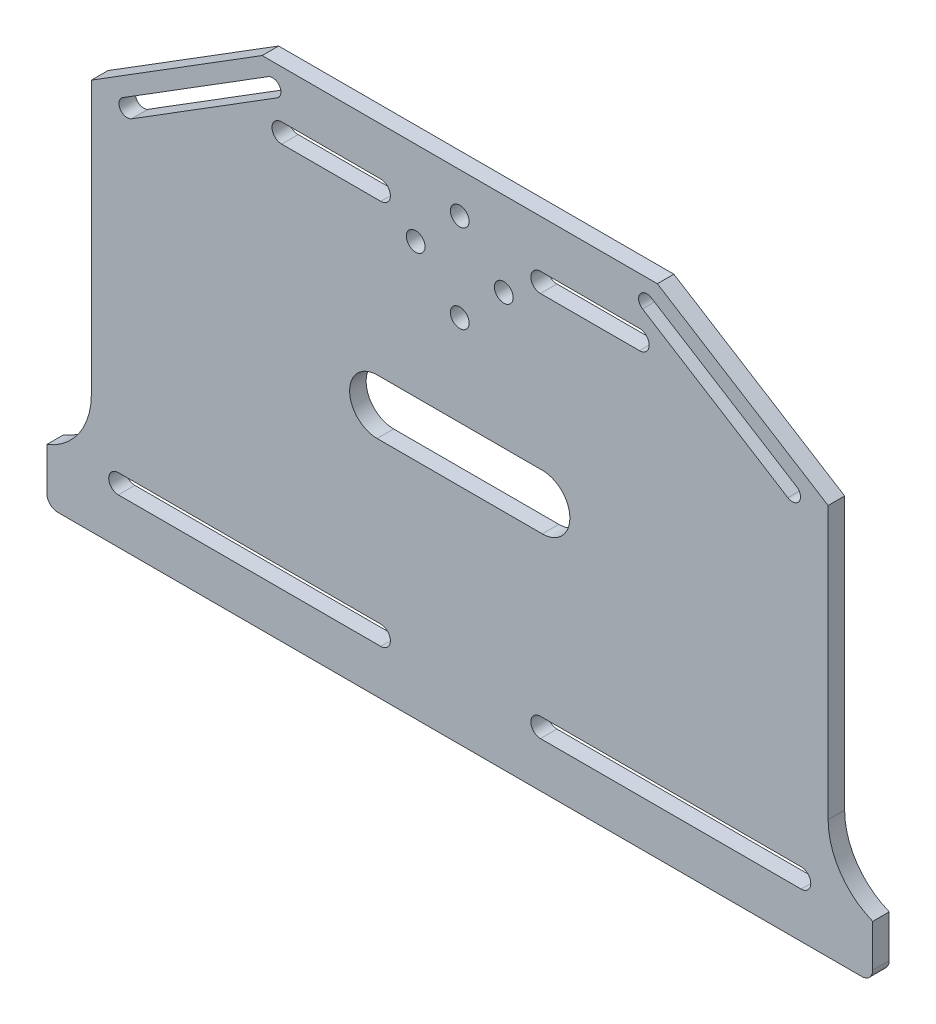
SolidWorks part; units mm, degrees
ref_plane "前视基准面" through (0, 0, 0) normal (0, 0, 1) x (1, 0, 0)
ref_plane "上视基准面" through (0, 0, 0) normal (0, 1, 0) x (1, 0, 0)
ref_plane "右视基准面" through (0, 0, 0) normal (1, 0, 0) x (0, 0, -1)
sketch "草图1" plane through (0, 0, 0) normal (0, 0, 1) x (1, 0, 0)
  line L0 (0, 148.5) -> (0, -94.9538) construction
  line L1 (105, -148.5) -> (-105, -148.5) construction
  line L2 (105, -148.5) -> (105, 148.5) construction
  line L3 (105, 148.5) -> (-105, 148.5) construction
  line L4 (-105, -148.5) -> (-105, 148.5) construction
  line L5 (105, -148.5) -> (-105, 148.5) construction
  line L6 (105, 148.5) -> (-105, -148.5) construction
  line L7 (35.8892, 121.6645) -> (-35.8892, 121.6645)
  line L8 (-35.8892, 121.6645) -> (-66.9017, 102.292)
  line L9 (-75, 40.9339) -> (-75, 31.2613)
  line L10 (-66.9017, 102.292) -> (-66.9017, 52.8701)
  line L11 (75, 40.9339) -> (75, 31.2613)
  line L12 (66.9017, 102.292) -> (66.9017, 52.8701)
  line L13 (35.8892, 121.6645) -> (66.9017, 102.292)
  line L14 (-75, 31.2613) -> (75, 31.2613)
  line L15 (-60, -148.5) -> (-60, -91.8129)
  line L16 (-75, 23.94) -> (75, 23.94)
  line L17 (-75, 23.94) -> (-75, 10.5626)
  line L18 (-38.8455, -105.5906) -> (-66.4608, -113.7617)
  line L19 (-66.4608, -113.7617) -> (-70.1743, -102.7328)
  line L20 (75, 23.94) -> (75, 10.5626)
  line L21 (66.4608, -113.7617) -> (70.1743, -102.7328)
  line L22 (38.8455, -105.5906) -> (66.4608, -113.7617)
  line L23 (-105, 93.0519) -> (105, 93.0519)
  line L24 (-105, 63.0519) -> (105, 63.0519)
  line L25 (-105, -90.0629) -> (-70.5337, -90.0629)
  line L26 (-105, -60.0629) -> (-67.4027, -60.0629)
  line L27 (60, -148.5) -> (60, 148.5)
  line L28 (-60, -58.3129) -> (-45, -58.3129)
  line L29 (-60, -61.8129) -> (-45, -61.8129)
  line L30 (-36, -58.3129) -> (-21, -58.3129)
  line L31 (-36, -61.8129) -> (-21, -61.8129)
  line L32 (-60, -88.3129) -> (-45, -88.3129)
  line L33 (-60, -91.8129) -> (-45, -91.8129)
  line L34 (-36, -88.3129) -> (-21, -88.3129)
  line L35 (-36, -91.8129) -> (-21, -91.8129)
  line L36 (-60, -58.3129) -> (-60, 148.5)
  line L37 (-19.25, -90.0629) -> (105, -90.0629)
  line L38 (-19.25, -60.0629) -> (19.25, -60.0629)
  line L39 (-60, -88.3129) -> (-60, -61.8129)
  line L40 (21, -58.3129) -> (36, -58.3129)
  line L41 (45, -58.3129) -> (60, -58.3129)
  line L42 (60, -61.8129) -> (45, -61.8129)
  line L43 (36, -61.8129) -> (21, -61.8129)
  line L44 (21, -88.3129) -> (36, -88.3129)
  line L45 (21, -91.8129) -> (36, -91.8129)
  line L46 (45, -88.3129) -> (60, -88.3129)
  line L47 (45, -91.8129) -> (60, -91.8129)
  line L48 (37.75, -60.0629) -> (43.25, -60.0629)
  line L49 (58.25, -60.0629) -> (105, -60.0629)
  line L50 (-60, 94.8019) -> (-45, 94.8019)
  line L51 (-36, 94.8019) -> (-21, 94.8019)
  line L52 (-60, 91.3019) -> (-45, 91.3019)
  line L53 (-36, 91.3019) -> (-21, 91.3019)
  line L54 (-60, 64.8019) -> (-45, 64.8019)
  line L55 (-60, 61.3019) -> (-45, 61.3019)
  line L56 (-36, 64.8019) -> (-21, 64.8019)
  line L57 (-36, 61.3019) -> (-21, 61.3019)
  line L58 (21, 94.8019) -> (36, 94.8019)
  line L59 (21, 91.3019) -> (36, 91.3019)
  line L60 (45, 94.8019) -> (60, 94.8019)
  line L61 (45, 91.3019) -> (60, 91.3019)
  line L62 (21, 61.3019) -> (36, 61.3019)
  line L63 (21, 64.8019) -> (36, 64.8019)
  line L64 (45, 61.3019) -> (60, 61.3019)
  line L65 (45, 64.8019) -> (60, 64.8019)
  line L66 (-33.1709, -104.7687) -> (33.1709, -104.7687)
  line L67 (0, -104.7687) -> (0, -148.5) construction
  arc A0 (-75, 40.9339) -> (-66.9017, 52.8701) centre (-79.7474, 52.8701) ccw
  arc A1 (75, 40.9339) -> (66.9017, 52.8701) centre (79.7474, 52.8701) cw
  arc A3 (-60, -88.3129) -> (-60, -91.8129) centre (-60, -90.0629) ccw
  arc A4 (-60, -58.3129) -> (-60, -61.8129) centre (-60, -60.0629) ccw
  circle A5 centre (-60, 63.0519) radius 1.75
  circle A6 centre (-60, 93.0519) radius 1.75
  circle A7 centre (60, 93.0519) radius 1.75
  circle A8 centre (60, 63.0519) radius 1.75
  arc A9 (60, -91.8129) -> (60, -88.3129) centre (60, -90.0629) ccw
  arc A10 (60, -61.8129) -> (60, -58.3129) centre (60, -60.0629) ccw
  arc A11 (-36, -58.3129) -> (-36, -61.8129) centre (-36, -60.0629) ccw
  arc A12 (-36, -88.3129) -> (-36, -91.8129) centre (-36, -90.0629) ccw
  arc A13 (36, -61.8129) -> (36, -58.3129) centre (36, -60.0629) ccw
  arc A14 (36, -91.8129) -> (36, -88.3129) centre (36, -90.0629) ccw
  arc A15 (-45, -61.8129) -> (-45, -58.3129) centre (-45, -60.0629) ccw
  arc A16 (-21, -61.8129) -> (-21, -58.3129) centre (-21, -60.0629) ccw
  arc A17 (-45, -91.8129) -> (-45, -88.3129) centre (-45, -90.0629) ccw
  arc A18 (-21, -91.8129) -> (-21, -88.3129) centre (-21, -90.0629) ccw
  arc A19 (45, -58.3129) -> (45, -61.8129) centre (45, -60.0629) ccw
  arc A20 (21, -58.3129) -> (21, -61.8129) centre (21, -60.0629) ccw
  arc A21 (21, -88.3129) -> (21, -91.8129) centre (21, -90.0629) ccw
  arc A22 (45, -88.3129) -> (45, -91.8129) centre (45, -90.0629) ccw
  circle A23 centre (-36, 93.0519) radius 1.75
  circle A24 centre (-36, 63.0519) radius 1.75
  circle A25 centre (36, 93.0519) radius 1.75
  circle A26 centre (36, 63.0519) radius 1.75
  circle A27 centre (-45, 93.0519) radius 1.75
  circle A28 centre (-21, 93.0519) radius 1.75
  circle A29 centre (-45, 63.0519) radius 1.75
  circle A30 centre (-21, 63.0519) radius 1.75
  circle A31 centre (21, 93.0519) radius 1.75
  circle A32 centre (21, 63.0519) radius 1.75
  circle A33 centre (45, 93.0519) radius 1.75
  circle A34 centre (45, 63.0519) radius 1.75
  arc A35 (33.1709, -104.7687) -> (38.8455, -105.5906) centre (33.1709, -124.7687) cw
  arc A36 (-33.1709, -104.7687) -> (-38.8455, -105.5906) centre (-33.1709, -124.7687) ccw
  spline S0 degree 3 poles (-75, 10.5626) (-72.6959, 1.9073) (-70.3396, -13.3728) (-67.1028, -43.6255) (-66.7657, -72.9327) (-71.8903, -95.1489) (-70.1743, -102.7328) knots 0 0 0 0 0.235247 0.406294 0.801186 1 1 1 1
  spline S1 degree 3 poles (75, 10.5626) (72.6959, 1.9073) (70.3396, -13.3728) (67.1028, -43.6255) (66.7657, -72.9327) (71.8903, -95.1489) (70.1743, -102.7328) knots 0 0 0 0 0.235247 0.406294 0.801186 1 1 1 1
  point P0 (0, 0)
  point P27 (0, 121.6645)
  point P42 (0, -94.0966)
  dimension "D1" = 60
  dimension "D4" = 20
  dimension "D5" = 24
  dimension "D7" = 24
  dimension "D9" = 15
  dimension "D10" = 15
  dimension "D13" = 24
  dimension "D17" = 15
  dimension "D2" = 30
  dimension "D3" = 30
  dimension "D6" = 24
  dimension "D8" = 24
  dimension "D11" = 15
  dimension "D12" = 15
  dimension "D14" = 24
  dimension "D15" = 24
  dimension "D16" = 24
  dimension "D18" = 15
  dimension "D19" = 15
  dimension "D20" = 15
  dimension "D21" = 15
  dimension "D22" = 15
  dimension "D23" = 15
  dimension "D24" = 15
  dimension "D25" = 15
  dimension "D26" = 15
  dimension "D27" = 15
  dimension "D28" = 15
  dimension "D29" = 3.5
  dimension "D30" = 3.5
  dimension "D31" = 3.5
extrude "凸台-拉伸1" add sketch "草图1" along normal blind 3
sketch "草图7" plane through (0, 0, 0) normal (0, 0, -1) x (-1, 0, 0)
  line L0 (0, 121.6645) -> (0, -104.7687) construction
  line L1 (-35.8892, 121.6645) -> (35.8892, 121.6645) construction
  line L2 (33.1709, -104.7687) -> (-33.1709, -104.7687) construction
  line L3 (0, 41.2613) -> (-21, 41.2613) construction
  line L4 (0, 41.2613) -> (21, 41.2613) construction
  line L5 (0, 13.94) -> (-21, 13.94) construction
  line L6 (0, 13.94) -> (21, 13.94) construction
  line L7 (75, 23.94) -> (-75, 23.94) construction
  line L8 (75, 31.2613) -> (-75, 31.2613) construction
  circle A0 centre (-21, 41.2613) radius 1.75
  circle A1 centre (21, 41.2613) radius 1.75
  circle A2 centre (-21, 13.94) radius 2.25
  circle A3 centre (21, 13.94) radius 2.25
  dimension "D1" = 10
  dimension "D2" = 10
extrude "切除-拉伸2" cut sketch "草图7" against normal through all
sketch "草图9" plane through (0, 0, 3) normal (0, 0, 1) x (1, 0, 0)
  line L0 (-70.7828, -98.747) -> (70.7828, -98.747) construction
  line L1 (0, -98.747) -> (0, -104.7687) construction
  line L2 (55, -100.497) -> (20, -100.497)
  line L3 (-55, -96.997) -> (-20, -96.997)
  line L4 (-55, -100.497) -> (-20, -100.497)
  line L5 (-33.1709, -104.7687) -> (33.1709, -104.7687) construction
  line L6 (55, -96.997) -> (20, -96.997)
  arc A0 (-55, -96.997) -> (-55, -100.497) centre (-55, -98.747) ccw
  arc A1 (-20, -100.497) -> (-20, -96.997) centre (-20, -98.747) ccw
  arc A2 (20, -100.497) -> (20, -96.997) centre (20, -98.747) cw
  arc A3 (55, -96.997) -> (55, -100.497) centre (55, -98.747) cw
  spline S0 degree 3 poles (-75, 10.5626) (-72.6959, 1.9073) (-70.3396, -13.3728) (-67.1028, -43.6255) (-66.7657, -72.9327) (-71.8903, -95.1489) (-70.1743, -102.7328) knots 0 0 0 0 0.235247 0.406294 0.801186 1 1 1 1 construction
  spline S1 degree 3 poles (75, 10.5626) (72.6959, 1.9073) (70.3396, -13.3728) (67.1028, -43.6255) (66.7657, -72.9327) (71.8903, -95.1489) (70.1743, -102.7328) knots 0 0 0 0 0.235247 0.406294 0.801186 1 1 1 1 construction
  dimension "D1" = 35
  dimension "D2" = 20
extrude "切除-拉伸4" cut sketch "草图9" against normal blind 3
sketch "草图10" plane through (0, 0, 3) normal (0, 0, 1) x (1, 0, 0)
  line L0 (-21, -60.0629) -> (-21, -90.0629) construction
  line L1 (21, -60.0629) -> (21, -90.0629) construction
  line L2 (-21, -75.0629) -> (-17.5, -75.0629) construction
  line L4 (12.5, -80.0629) -> (-12.5, -80.0629)
  line L6 (12.5, -70.0629) -> (-12.5, -70.0629)
  line L11 (17.5, -75.0629) -> (21, -75.0629) construction
  arc A0 (-12.5, -70.0629) -> (-12.5, -80.0629) centre (-12.5, -75.0629) ccw
  arc A1 (12.5, -80.0629) -> (12.5, -70.0629) centre (12.5, -75.0629) ccw
  point P11 (0, -75.0629)
extrude "切除-拉伸5" cut sketch "草图10" against normal blind 3
sketch "草图11" plane through (0, 0, 3) normal (0, 0, 1) x (1, 0, 0)
  line L0 (-21, 93.0519) -> (-21, 63.0519) construction
  line L1 (21, 93.0519) -> (21, 63.0519) construction
  line L2 (-21, 78.0519) -> (-20, 78.0519) construction
  line L4 (15, 73.0519) -> (-15, 73.0519)
  line L6 (15, 83.0519) -> (-15, 83.0519)
  line L10 (20, 78.0519) -> (21, 78.0519) construction
  arc A0 (-15, 83.0519) -> (-15, 73.0519) centre (-15, 78.0519) ccw
  arc A1 (15, 73.0519) -> (15, 83.0519) centre (15, 78.0519) ccw
  point P10 (0, 78.0519)
  dimension "D1" = 30
extrude "切除-拉伸8" cut sketch "草图11" against normal blind 3
sketch "草图12" plane through (0, 0, 3) normal (0, 0, 1) x (1, 0, 0)
  line L0 (0, 121.6645) -> (0, 83.0519) construction
  line L1 (35.8892, 121.6645) -> (-35.8892, 121.6645) construction
  line L2 (15, 83.0519) -> (-15, 83.0519) construction
  circle A0 centre (0, 106.3718) radius 11 construction
  circle A1 centre (0, 106.3718) radius 8 construction
  circle A2 centre (0, 114.3718) radius 1.7
  circle A3 centre (0, 98.3718) radius 1.7
  circle A4 centre (8, 106.3718) radius 1.7
  circle A5 centre (-8, 106.3718) radius 1.7
extrude "切除-拉伸9" cut sketch "草图12" against normal blind 3
sketch "草图13" plane through (0, 0, 3) normal (0, 0, 1) x (1, 0, 0)
  line L0 (0, -104.7687) -> (0, -80.0629) construction
  line L1 (-33.1709, -104.7687) -> (33.1709, -104.7687) construction
  line L2 (-12.5, -80.0629) -> (12.5, -80.0629) construction
  circle A0 centre (0, -92.4158) radius 8 construction
  circle A1 centre (0, -84.4158) radius 1.7
  circle A2 centre (8, -92.4158) radius 1.7
  circle A3 centre (0, -100.4158) radius 1.7
  circle A4 centre (-8, -92.4158) radius 1.7
extrude "切除-拉伸11" cut sketch "草图13" against normal blind 3
sketch "草图14" plane through (0, 0, 3) normal (0, 0, 1) x (1, 0, 0)
  line L0 (0, 23.94) -> (0, -104.7687) construction
  line L1 (-55.4755, 8.9197) -> (-55.4755, -46.0803)
  line L2 (-58.9755, 8.9197) -> (-58.9755, -46.0803)
  line L3 (-75, 23.94) -> (75, 23.94) construction
  line L4 (-33.1709, -104.7687) -> (33.1709, -104.7687) construction
  line L5 (58.9755, 8.9197) -> (58.9755, -46.0803)
  line L6 (55.4755, 8.9197) -> (55.4755, -46.0803)
  arc A0 (-55.4755, 8.9197) -> (-58.9755, 8.9197) centre (-57.2255, 8.9197) ccw
  arc A1 (-58.9755, -46.0803) -> (-55.4755, -46.0803) centre (-57.2255, -46.0803) ccw
  arc A2 (58.9755, -46.0803) -> (55.4755, -46.0803) centre (57.2255, -46.0803) cw
  arc A3 (55.4755, 8.9197) -> (58.9755, 8.9197) centre (57.2255, 8.9197) cw
extrude "切除-拉伸12" cut sketch "草图14" against normal through all
fillet "圆角1" radius 2 2 edges at (75, 31.2613, 1.5) (-75, 31.2613, 1.5)
fillet "圆角2" radius 2 2 edges at (-75, 23.94, 1.5) (75, 23.94, 1.5)
sketch "草图15" plane through (0, 0, 0) normal (0, 0, -1) x (-1, 0, 0)
  line L0 (0, 121.6645) -> (0, 31.2613) construction
  line L1 (-35.8892, 121.6645) -> (35.8892, 121.6645) construction
  line L2 (73, 31.2613) -> (-73, 31.2613) construction
  line L3 (-27.5188, 121.6645) -> (-63.6963, 99.0657) construction
  line L4 (-35.8892, 121.6645) -> (-66.9017, 102.292) construction
  line L5 (-61.1842, 102.4035) -> (-34.7748, 118.9006)
  line L6 (-59.5948, 99.8591) -> (-33.1854, 116.3562)
  line L7 (27.5188, 121.6645) -> (63.6963, 99.0657) construction
  line L8 (59.5948, 99.8591) -> (33.1854, 116.3562)
  line L9 (61.1842, 102.4035) -> (34.7748, 118.9006)
  arc A0 (-61.1842, 102.4035) -> (-59.5948, 99.8591) centre (-60.3895, 101.1313) ccw
  arc A1 (-33.1854, 116.3562) -> (-34.7748, 118.9006) centre (-33.9801, 117.6284) ccw
  arc A2 (33.1854, 116.3562) -> (34.7748, 118.9006) centre (33.9801, 117.6284) cw
  arc A3 (61.1842, 102.4035) -> (59.5948, 99.8591) centre (60.3895, 101.1313) cw
extrude "切除-拉伸13" cut sketch "草图15" against normal through all
sketch "草图16" plane through (0, 0, 0) normal (0, 0, -1) x (-1, 0, 0)
  line L0 (0, 121.6645) -> (0, 31.2613) construction
  line L1 (-35.8892, 121.6645) -> (35.8892, 121.6645) construction
  line L2 (73, 31.2613) -> (-73, 31.2613) construction
  line L3 (-21, 41.2613) -> (-66.71, 41.2613) construction
  line L4 (-62, 43.0113) -> (-32, 43.0113)
  line L5 (-62, 39.5113) -> (-32, 39.5113)
  line L6 (21, 41.2613) -> (66.71, 41.2613) construction
  line L7 (62, 39.5113) -> (32, 39.5113)
  line L8 (62, 43.0113) -> (32, 43.0113)
  line L9 (-75, 40.9339) -> (-75, 33.2613) construction
  arc A0 (-62, 43.0113) -> (-62, 39.5113) centre (-62, 41.2613) ccw
  arc A1 (-32, 39.5113) -> (-32, 43.0113) centre (-32, 41.2613) ccw
  arc A2 (32, 39.5113) -> (32, 43.0113) centre (32, 41.2613) cw
  arc A3 (62, 43.0113) -> (62, 39.5113) centre (62, 41.2613) cw
  dimension "D2" = 13
sketch "草图17" plane through (0, 0, 0) normal (0, 0, -1) x (-1, 0, 0)
  text T0 "Y" font "黑体" height in points 72
extrude "切除-拉伸15" cut sketch "草图17" against normal through all
sketch "草图18" plane through (0, 0, 0) normal (0, 0, -1) x (-1, 0, 0)
  text T0 "H" font "黑体" height in points 72
extrude "切除-拉伸16" cut sketch "草图18" against normal through all
sketch "草图20" plane through (0, 0, 0) normal (0, 0, -1) x (-1, 0, 0)
  line L0 (-66.9017, 102.292) -> (-66.9017, 52.8701) construction
  line L1 (-66.9017, 95.8596) -> (66.9017, 95.8596)
  line L2 (-66.9017, 95.8596) -> (-66.9017, 52.8701)
  line L3 (-66.9017, 52.8701) -> (66.9017, 52.8701)
  line L4 (66.9017, 95.8596) -> (66.9017, 52.8701)
extrude "凸台-拉伸2" add sketch "草图20" against normal blind 3
sketch "草图21" plane through (0, 0, 0) normal (0, 0, -1) x (-1, 0, 0)
  line L1 (-64.7663, -56.4228) -> (64.4409, -56.4228)
  line L2 (-64.7663, -56.4228) -> (-64.7663, -95.2117)
  line L3 (-64.7663, -95.2117) -> (64.4409, -95.2117)
  line L4 (64.4409, -56.4228) -> (64.4409, -95.2117)
extrude "凸台-拉伸3" add sketch "草图21" against normal blind 3
sketch "草图22" plane through (0, 0, 0) normal (0, 0, -1) x (-1, 0, 0)
  line L1 (-46.7188, -3.1128) -> (-25.8503, -3.1128)
  line L2 (-46.7188, -3.1128) -> (-46.7188, -34.3233)
  line L3 (-46.7188, -34.3233) -> (-25.8503, -34.3233)
  line L4 (-25.8503, -3.1128) -> (-25.8503, -34.3233)
  line L5 (28.8143, -3.1128) -> (49.8675, -3.1128)
  line L6 (28.8143, -3.1128) -> (28.8143, -33.2152)
  line L7 (28.8143, -33.2152) -> (49.8675, -33.2152)
  line L8 (49.8675, -3.1128) -> (49.8675, -33.2152)
extrude "凸台-拉伸4" add sketch "草图22" against normal blind 3
sketch "草图24" plane through (0, 0, 0) normal (0, 0, -1) x (-1, 0, 0)
  line L1 (-64.9961, 44.3276) -> (-28.6954, 44.3276)
  line L2 (-64.9961, 44.3276) -> (-64.9961, 38.3743)
  line L3 (-64.9961, 38.3743) -> (-28.6954, 38.3743)
  line L4 (-28.6954, 44.3276) -> (-28.6954, 38.3743)
  line L5 (29.2405, 44.3276) -> (65.8315, 44.3276)
  line L6 (29.2405, 44.3276) -> (29.2405, 38.3743)
  line L7 (29.2405, 38.3743) -> (65.8315, 38.3743)
  line L8 (65.8315, 44.3276) -> (65.8315, 38.3743)
extrude "凸台-拉伸5" add sketch "草图24" against normal blind 3
sketch "草图25" plane through (0, 0, 0) normal (0, 0, -1) x (-1, 0, 0)
  line L0 (-32.6582, 113.0113) -> (-14.6582, 113.0113)
  line L1 (-32.6582, 109.5113) -> (-14.6582, 109.5113)
  line L2 (-21, 41.2613) -> (21, 41.2613)
  line L3 (-0.3165, 111.2613) -> (0, 41.2613) construction
  line L4 (14.3418, 113.0113) -> (32.3418, 113.0113)
  line L5 (32.3418, 41.2613) -> (-32.6582, 41.2613)
  line L6 (32.3418, 41.2613) -> (32.3418, 111.2613)
  line L8 (-32.6582, 41.2613) -> (-32.6582, 111.2613)
  line L9 (32.3418, 41.2613) -> (-32.6582, 111.2613) construction
  line L10 (30.7168, 109.5113) -> (-32.6582, 41.2613) construction
  line L11 (14.3418, 109.5113) -> (32.3418, 109.5113)
  line L12 (32.3418, 76.2613) -> (-32.6582, 76.2613) construction
  line L13 (12.5918, 111.2613) -> (-12.9082, 111.2613)
  line L14 (12.5918, 41.2613) -> (-12.9082, 41.2613)
  line L15 (14.3418, 43.0113) -> (32.3418, 43.0113)
  line L16 (14.3418, 39.5113) -> (32.3418, 39.5113)
  line L17 (-32.6582, 43.0113) -> (-14.6582, 43.0113)
  line L18 (-32.6582, 39.5113) -> (-14.6582, 39.5113)
  circle A0 centre (-32.6582, 111.2613) radius 1.75
  arc A1 (32.3418, 109.5113) -> (32.3418, 113.0113) centre (32.3418, 111.2613) ccw
  arc A2 (-14.6582, 109.5113) -> (-14.6582, 113.0113) centre (-14.6582, 111.2613) ccw
  arc A3 (14.3418, 113.0113) -> (14.3418, 109.5113) centre (14.3418, 111.2613) ccw
  arc A4 (14.3418, 39.5113) -> (14.3418, 43.0113) centre (14.3418, 41.2613) cw
  arc A5 (-14.6582, 43.0113) -> (-14.6582, 39.5113) centre (-14.6582, 41.2613) cw
  arc A6 (32.3418, 43.0113) -> (32.3418, 39.5113) centre (32.3418, 41.2613) cw
  circle A7 centre (-32.6582, 41.2613) radius 1.75
  point P9 (-0.1582, 76.2613)
  dimension "D1" = 18
  dimension "D2" = 18
extrude "切除-拉伸17" cut sketch "草图25" against normal through all
extrude "切除-拉伸19" cut sketch "草图16" against normal through all
sketch "草图26" plane through (0, 0, 0) normal (0, 0, -1) x (-1, 0, 0)
  line L0 (0, 121.6645) -> (0, -104.7687) construction
  line L1 (-35.8892, 121.6645) -> (35.8892, 121.6645) construction
  line L2 (33.1709, -104.7687) -> (-33.1709, -104.7687) construction
  line L4 (15, 71.877) -> (-15, 71.877)
  line L6 (15, 81.877) -> (-15, 81.877)
  arc A0 (-15, 81.877) -> (-15, 71.877) centre (-15, 76.877) ccw
  arc A1 (15, 71.877) -> (15, 81.877) centre (15, 76.877) ccw
  point P6 (0, 76.877)
extrude "切除-拉伸20" cut sketch "草图26" against normal through all
sketch "草图27" plane through (0, 0, 0) normal (0, 0, -1) x (-1, 0, 0)
  line L0 (0, 23.94) -> (0, -104.7687) construction
  line L1 (73, 23.94) -> (-73, 23.94) construction
  line L2 (33.1709, -104.7687) -> (-33.1709, -104.7687) construction
  line L3 (-42.5, -15.81) -> (-10, -15.81)
  line L4 (42.5, -17.56) -> (-42.5, -17.56)
  line L5 (42.5, -17.56) -> (42.5, 5.44)
  line L6 (42.5, 5.44) -> (-42.5, 5.44)
  line L7 (-42.5, -17.56) -> (-42.5, 5.44)
  line L8 (42.5, -17.56) -> (-42.5, 5.44) construction
  line L9 (42.5, 5.44) -> (-42.5, -17.56) construction
  line L10 (-42.5, -19.31) -> (-10, -19.31)
  line L11 (-42.5, 7.19) -> (-10, 7.19)
  line L12 (-42.5, 3.69) -> (-10, 3.69)
  line L13 (10, 7.19) -> (42.5, 7.19)
  line L14 (10, 3.69) -> (42.5, 3.69)
  line L15 (10, -15.81) -> (42.5, -15.81)
  line L16 (10, -19.31) -> (42.5, -19.31)
  circle A0 centre (-42.5, 5.44) radius 1.75
  circle A1 centre (-42.5, -17.56) radius 1.75
  circle A2 centre (42.5, 5.44) radius 1.75
  circle A3 centre (42.5, -17.56) radius 1.75
  circle A4 centre (-10, 5.44) radius 1.75
  circle A5 centre (-10, -17.56) radius 1.75
  circle A6 centre (10, -17.56) radius 1.75
  circle A7 centre (10, 5.44) radius 1.75
  point P6 (0, -6.06)
  dimension "D4" = 10
  dimension "D5" = 10
  dimension "D1" = 30
  dimension "D2" = 85
  dimension "D3" = 23
extrude "切除-拉伸21" cut sketch "草图27" against normal through all contours L6 A0 L7 | L7 A0 L6 | A4 L11 A0 L6 | A4 L6 A0 L12 | L6 A4 | L6 A4 | A7 L6 | A7 L6 | L6 A7 L14 A2 | L13 A7 L6 A2 | A2 L6 L5 | L6 A2 L5 | L7 A1 L4 | L4 A1 L7 | A5 L3 A1 L4 | A5 L4 A1 L10 | L4 A5 | L4 A5 | A6 L4 | A6 L4 | L4 A6 L16 A3 | L15 A6 L4 A3 | L4 A3 L5 | L5 A3 L4
sketch "草图28" plane through (0, 0, 0) normal (0, 0, -1) x (-1, 0, 0)
  line L0 (0, 23.94) -> (0, -104.7687) construction
  line L1 (73, 23.94) -> (-73, 23.94) construction
  line L2 (33.1709, -104.7687) -> (-33.1709, -104.7687) construction
  arc A0 (0, -48.8123) -> (-10.2848, -54.2659) centre (-5.1424, -51.5391) ccw
  arc A1 (-10.2848, -54.2659) -> (0, -63.7557) centre (7.9187, -44.8556) ccw
  arc A2 (10.2848, -54.2659) -> (0, -63.7557) centre (-7.9187, -44.8556) cw
  arc A3 (0, -48.8123) -> (10.2848, -54.2659) centre (5.1424, -51.5391) cw
extrude "切除-拉伸22" cut sketch "草图28" against normal through all
sketch "草图29" plane through (0, 0, 0) normal (0, 0, -1) x (-1, 0, 0)
  line L0 (0, 23.94) -> (0, -104.7687) construction
  line L1 (73, 23.94) -> (-73, 23.94) construction
  line L2 (33.1709, -104.7687) -> (-33.1709, -104.7687) construction
  arc A0 (-21.3687, -73.4908) -> (21.3687, -73.4908) centre (0, -58.7579) ccw
  arc A1 (-24.1996, -75.4426) -> (24.1996, -75.4426) centre (0, -58.7579) ccw
  arc A2 (-21.3687, -73.4908) -> (-24.1996, -75.4426) centre (-22.7842, -74.4667) ccw
  arc A3 (24.1996, -75.4426) -> (21.3687, -73.4908) centre (22.7842, -74.4667) ccw
extrude "切除-拉伸23" cut sketch "草图29" against normal blind 3
sketch "草图30" plane through (0, 0, 3) normal (0, 0, 1) x (1, 0, 0)
  line L1 (-82.3693, 26.4895) -> (90.8008, 26.4895)
  line L2 (-82.3693, 26.4895) -> (-82.3693, -123.6562)
  line L3 (-82.3693, -123.6562) -> (90.8008, -123.6562)
  line L4 (90.8008, 26.4895) -> (90.8008, -123.6562)
extrude "切除-拉伸24" cut sketch "草图30" against normal blind 10
